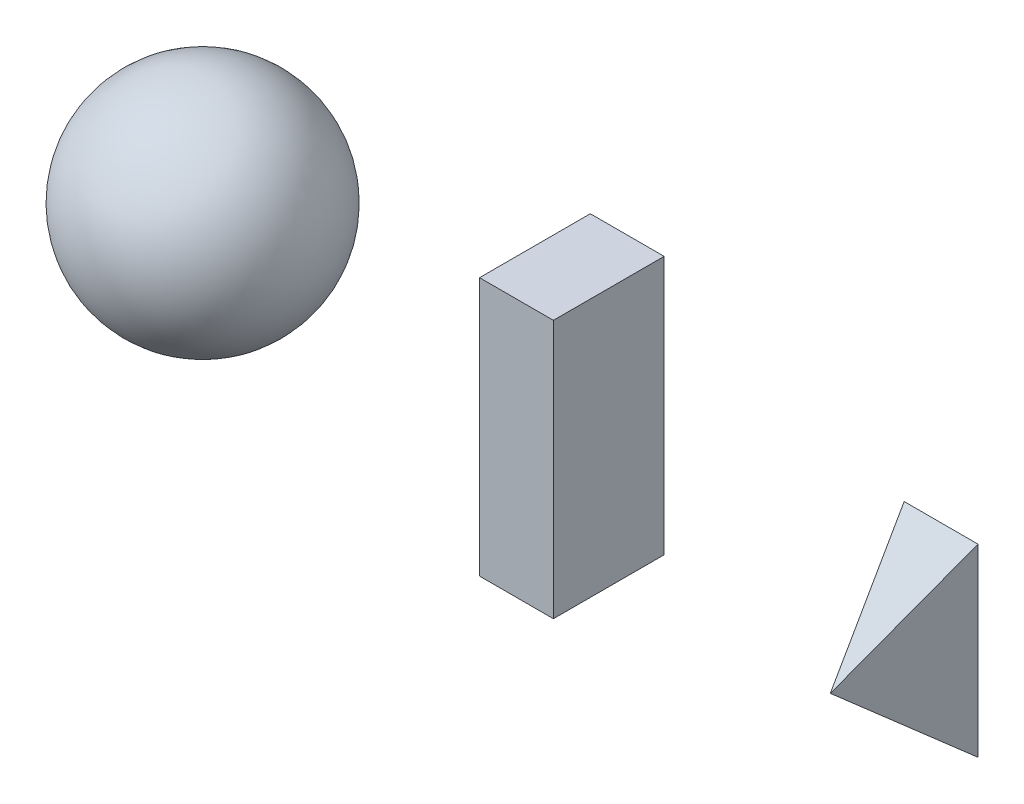
SolidWorks part; units mm, degrees
ref_plane "Front Plane" through (0, 0, 0) normal (0, 0, 1) x (1, 0, 0)
ref_plane "Top Plane" through (0, 0, 0) normal (0, 1, 0) x (1, 0, 0)
ref_plane "Right Plane" through (0, 0, 0) normal (1, 0, 0) x (0, 0, -1)
sketch "Sketch1" plane through (0, 0, 0) normal (0, 0, 1) x (1, 0, 0)
  line L1 (-25.4, -88.9) -> (25.4, -88.9)
  line L2 (-25.4, -88.9) -> (-25.4, 88.9)
  line L3 (-25.4, 88.9) -> (25.4, 88.9)
  line L4 (25.4, -88.9) -> (25.4, 88.9)
  line L5 (-25.4, -88.9) -> (25.4, 88.9) construction
  line L6 (-25.4, 88.9) -> (25.4, -88.9) construction
  point P0 (0, 0)
  dimension "D1" = 50.8
  dimension "D2" = 177.8
extrude "RecPrism" add sketch "Sketch1" along normal mid plane 76.2
sketch "Sphere" plane through (0, 0, 0) normal (0, 0, 1) x (1, 0, 0)
  line L1 (-254, 76.2) -> (-254, 0)
  line L2 (-254, 0) -> (-254, -76.2)
  arc A0 (-254, 76.2) -> (-254, -76.2) centre (-254, 0) ccw
  point P4 (0, 0)
  dimension "D1" = 76.2
  dimension "D2" = 254
sketch "PyramidBase" plane through (0, 0, 0) normal (0, 0, 1) x (1, 0, 0)
  line L1 (228.6, -63.5) -> (279.4, -63.5)
  line L2 (228.6, -63.5) -> (228.6, 63.5)
  line L3 (228.6, 63.5) -> (279.4, 63.5)
  line L4 (279.4, -63.5) -> (279.4, 63.5)
  line L5 (228.6, -63.5) -> (279.4, 63.5) construction
  line L6 (228.6, 63.5) -> (279.4, -63.5) construction
  point P0 (254, 0)
  dimension "D1" = 50.8
  dimension "D2" = 127
  dimension "D3" = 254
ref_plane "PyramidPlane" through (254, 0, 0) normal (1, 0, 0) x (0, 0, -1)
sketch "PyramidHeight" plane through (254, 0, 0) normal (1, 0, 0) x (0, 0, -1)
  line L0 (0, 0) -> (-76.2, 0)
  dimension "D1" = 76.2
extrude "Pyramid" add sketch "PyramidBase" along normal up to vertex (76.2 mm away) separate body up to point (254, 0, 76.2)
sketch "Sketch5" plane through (0, 0, 0) normal (0, 1, 0) x (1, 0, 0)
  line L0 (279.4, 0) -> (254, -76.2)
  line L1 (279.4, -76.2) -> (228.6, -76.2) construction
  line L2 (254, -76.2) -> (228.6, 0)
  line L3 (228.6, 0) -> (279.4, 0)
extrude "Cut-Extrude_PyramidY" cut sketch "Sketch5" against normal through all both and the other way through all flip side to cut
sketch "Sketch6" plane through (254, 0, 0) normal (1, 0, 0) x (0, 0, -1)
  line L0 (-76.2, 0) -> (0, 63.5)
  line L1 (0, 63.5) -> (0, -63.5)
  line L2 (0, -63.5) -> (-76.2, 0)
extrude "Cut-Extrude_PyramidX" cut sketch "Sketch6" against normal through all both and the other way through all flip side to cut
revolve "SphereRevolve" add sketch "Sphere" angle 360 about L1
equation "\"sphere_radius\" = 3"
equation "\"prism_length\" = 7"
equation "\"prism_width\" = 2"
equation "\"prism_height\" = 3"
equation "\"pyramid_length\" = 2"
equation "\"pyramid_width\" = 5"
equation "\"pyramid_height\" = 3"
equation "\"D1@Sketch1\"=\"prism_width\""
equation "\"D2@Sketch1\"=\"prism_length\""
equation "\"D1@RecPrism\"=\"prism_height\""
equation "\"D1@PyramidBase\"=\"pyramid_length\""
equation "\"D2@PyramidBase\"=\"pyramid_width\""
equation "\"D1@PyramidHeight\"=\"pyramid_height\""
equation "\"D1@Sphere\"=\"sphere_radius\""
